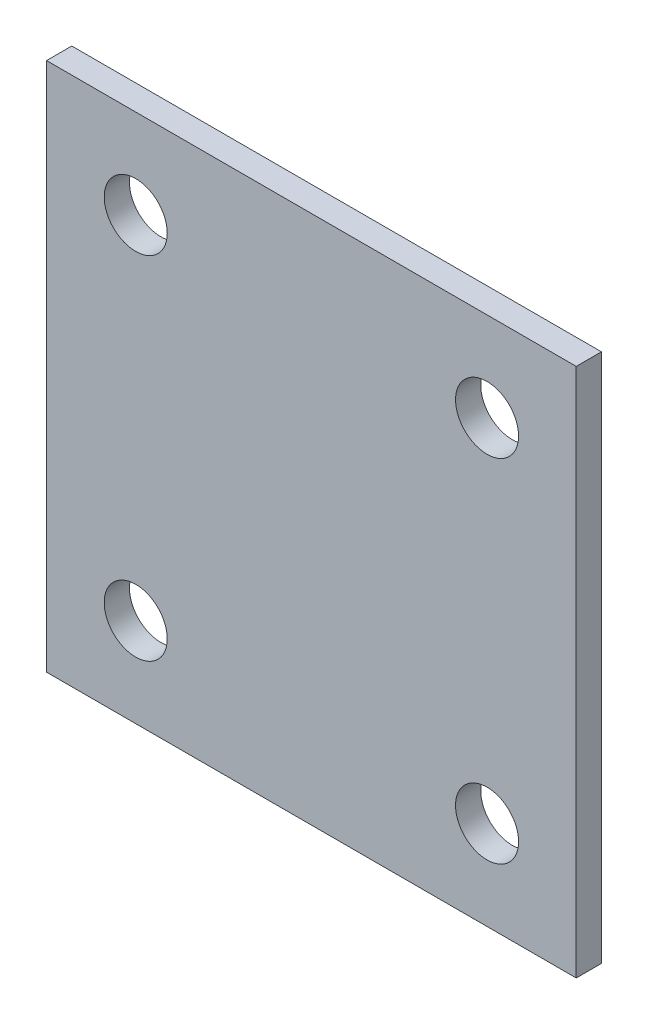
SolidWorks part; units mm, degrees
ref_plane "Front Plane" through (0, 0, 0) normal (0, 0, 1) x (1, 0, 0)
ref_plane "Top Plane" through (0, 0, 0) normal (0, 1, 0) x (1, 0, 0)
ref_plane "Right Plane" through (0, 0, 0) normal (1, 0, 0) x (0, 0, -1)
sketch "Sketch1" plane through (0, 0, 0) normal (0, 0, 1) x (1, 0, 0)
  line L0 (-39.7306, 21.2098) -> (-21.7701, 3.2493) construction
  line L1 (-39.7306, 21.2098) -> (66.9494, 21.2098)
  line L2 (-39.7306, 21.2098) -> (-39.7306, -85.4702)
  line L3 (-39.7306, -85.4702) -> (66.9494, -85.4702)
  line L4 (66.9494, 21.2098) -> (66.9494, -85.4702)
  line L5 (-21.7701, 3.2493) -> (48.9889, -67.5096) construction
  line L6 (48.9889, -67.5096) -> (66.9494, -85.4702) construction
  line L7 (66.9494, 21.2098) -> (48.9889, 3.2493) construction
  line L8 (48.9889, 3.2493) -> (-21.7701, -67.5096) construction
  line L9 (-21.7701, -67.5096) -> (-39.7306, -85.4702) construction
  circle A0 centre (-21.7701, 3.2493) radius 6.35
  circle A1 centre (48.9889, 3.2493) radius 6.35
  circle A2 centre (-21.7701, -67.5096) radius 6.35
  circle A3 centre (48.9889, -67.5096) radius 6.35
  dimension "D1" = 106.68
extrude "Boss-Extrude1" add sketch "Sketch1" along normal blind 5.08
equation "\"D1@Sketch1\" = \"BoxWidth@BotBody.part\""
equation "\"D1@Boss-Extrude1\" = \"MDF@FinalBot.assembly\""
